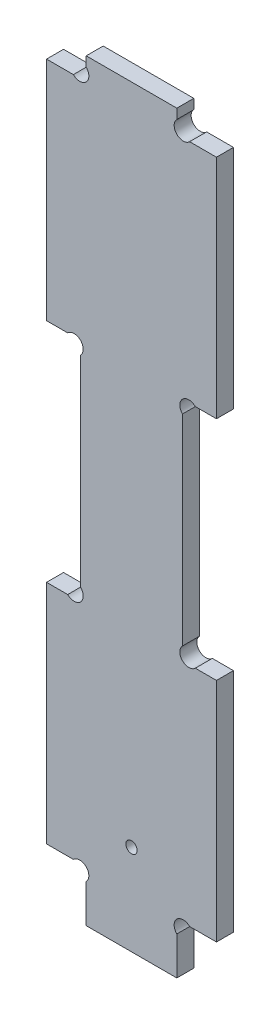
SolidWorks part; units mm, degrees
ref_plane "Plan de face" through (0, 0, 0) normal (0, 0, 1) x (1, 0, 0)
ref_plane "Plan de dessus" through (0, 0, 0) normal (0, 1, 0) x (1, 0, 0)
ref_plane "Plan de droite" through (0, 0, 0) normal (1, 0, 0) x (0, 0, -1)
sketch "Esquisse1" plane through (0, 0, 0) normal (0, 0, 1) x (1, 0, 0)
  line L14 (25.2627, 9) -> (30, 9)
  line L16 (30, 49) -> (30, 9)
  line L17 (26.2627, 49) -> (30, 49)
  line L18 (25.2627, 129) -> (30, 129)
  line L19 (30, 89) -> (30, 129)
  line L20 (26.2627, 89) -> (30, 89)
  line L21 (3.7373, 89) -> (0, 89)
  line L22 (0, 89) -> (0, 129)
  line L23 (4.7373, 129) -> (0, 129)
  line L24 (3.7373, 49) -> (0, 49)
  line L25 (0, 49) -> (0, 9)
  line L26 (4.7373, 9) -> (0, 9)
  line L27 (23, 131.2627) -> (23, 133)
  line L28 (23, 6.7373) -> (23, 0)
  line L29 (24, 86.7373) -> (24, 51.2627)
  line L30 (7, 131.2627) -> (7, 133)
  line L31 (6, 86.7373) -> (6, 51.2627)
  line L32 (7, 6.7373) -> (7, 0)
  line L33 (7, 133) -> (23, 133)
  line L34 (7, 0) -> (23, 0)
  arc A1 (25.2627, 9) -> (23, 6.7373) centre (24.1314, 7.8686) ccw
  arc A2 (24, 51.2627) -> (26.2627, 49) centre (25.1314, 50.1314) ccw
  arc A3 (25.2627, 129) -> (23, 131.2627) centre (24.1314, 130.1314) cw
  arc A5 (24, 86.7373) -> (26.2627, 89) centre (25.1314, 87.8686) cw
  arc A6 (6, 86.7373) -> (3.7373, 89) centre (4.8686, 87.8686) ccw
  arc A8 (4.7373, 129) -> (7, 131.2627) centre (5.8686, 130.1314) ccw
  arc A9 (6, 51.2627) -> (3.7373, 49) centre (4.8686, 50.1314) cw
  arc A10 (4.7373, 9) -> (7, 6.7373) centre (5.8686, 7.8686) cw
  point P2 (23.9214, 131.5877)
  point P4 (0, 0)
  dimension "D13" = 6
  dimension "D14" = 30
  dimension "D20" = 1.6
  dimension "D1" = 40
  dimension "D2" = 40
  dimension "D3" = 40
  dimension "D4" = 4
  dimension "D5" = 9
  dimension "D6" = 30
  dimension "D7" = 16
  dimension "D8" = 18
  dimension "D9" = 16
  dimension "D10" = 7
  dimension "D11" = 7
  dimension "D12" = 6
  dimension "D15" = 1.1314
  dimension "D16" = 1.1314
  dimension "D17" = 2.2627
  dimension "D18" = 2.2627
  dimension "D19" = 7
  dimension "D21" = 1.1314
  dimension "D22" = 1.1314
  dimension "D23" = 2.2627
  dimension "D24" = 2.2627
  dimension "D25" = 1.1314
  dimension "D26" = 2.2627
  dimension "D27" = 2.2627
  dimension "D28" = 1.1314
  dimension "D29" = 1.1314
  dimension "D30" = 1.1314
  dimension "D31" = 2.2627
  dimension "D32" = 2.2627
extrude "Extrusion1" add sketch "Esquisse1" along normal blind 3
sketch "Esquisse2" plane through (0, 0, 3) normal (0, 0, 1) x (1, 0, 0)
  line L0 (25.2627, 9) -> (30, 9) construction
  line L1 (7, 0) -> (23, 0) construction
  circle A0 centre (15, 16) radius 1
  point P4 (15, 0)
  point P5 (0, 0)
  dimension "D2" = 2
  dimension "D1" = 7
extrude "Enlèv. mat.-Extru.1" cut sketch "Esquisse2" against normal through all
